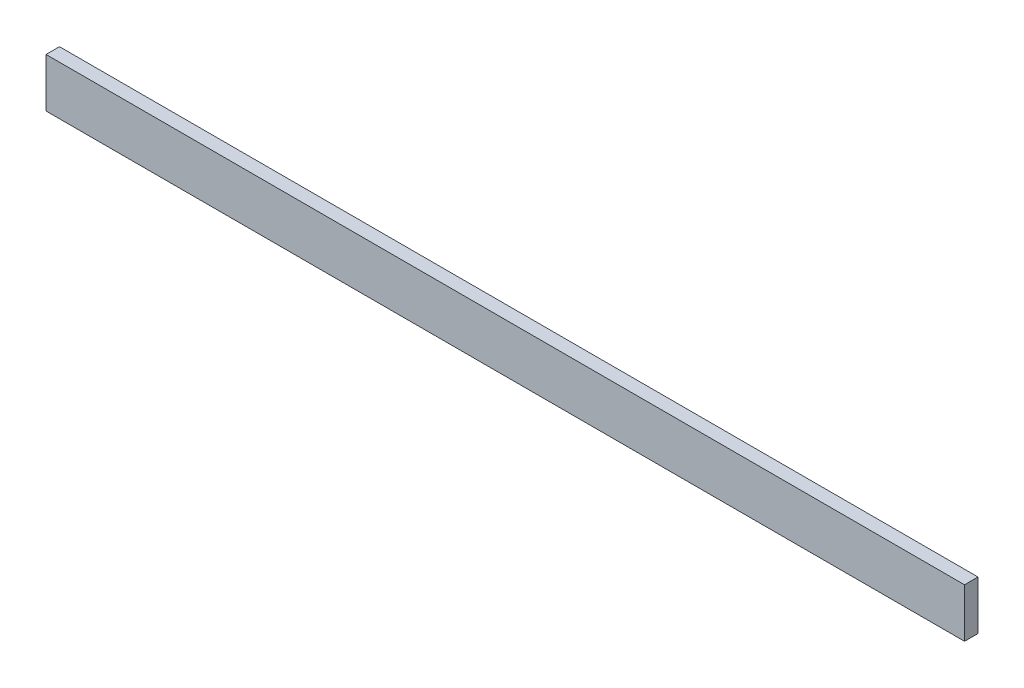
SolidWorks part; units mm, degrees
ref_plane "Face" through (0, 0, 0) normal (0, 0, 1) x (1, 0, 0)
ref_plane "Dessus" through (0, 0, 0) normal (0, 1, 0) x (1, 0, 0)
ref_plane "Droite" through (0, 0, 0) normal (1, 0, 0) x (0, 0, -1)
sketch "Esquisse1" plane through (0, 0, 0) normal (0, 0, 1) x (1, 0, 0)
  line L1 (0, 0) -> (1500, 0)
  line L2 (0, 0) -> (0, 80)
  line L3 (0, 80) -> (1500, 80)
  line L4 (1500, 0) -> (1500, 80)
  dimension "D1" = 1500
  dimension "D2" = 80
extrude "Extrusion1" add sketch "Esquisse1" along normal blind 22
